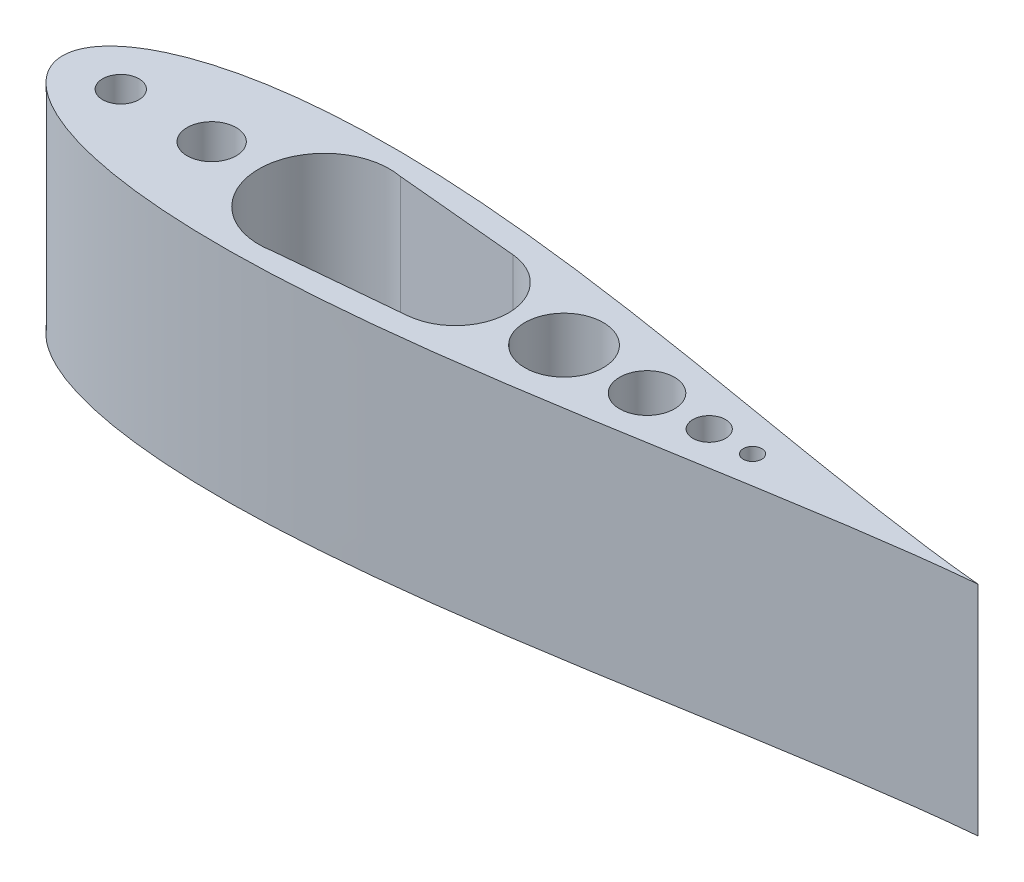
SolidWorks part; units mm, degrees
ref_plane "Front Plane" through (0, 0, 0) normal (0, 0, 1) x (1, 0, 0)
ref_plane "Top Plane" through (0, 0, 0) normal (0, 1, 0) x (1, 0, 0)
ref_plane "Right Plane" through (0, 0, 0) normal (1, 0, 0) x (0, 0, -1)
sketch "Sketch1" plane through (0, 0, 0) normal (0, 1, 0) x (1, 0, 0)
  line L0 (106.2646, 9.0063) -> (64.0952, 9.0063)
  line L4 (64.0952, 9.0063) -> (56.3694, 9.0063)
  line L5 (52.0514, 9.0063) -> (47.9363, 9.0063)
  line L6 (40.3163, 9.0063) -> (36.0359, 9.0063)
  line L7 (23.2512, 9.0063) -> (19.4412, 9.0063)
  line L8 (1.1792, 9.0063) -> (-2.6308, 9.0063)
  line L9 (-27.3546, 9.0063) -> (-31.1646, 9.0063)
  line L10 (-59.9171, 9.0063) -> (-65.1664, 9.0063)
  line L11 (-78.3744, 9.0063) -> (-87.6454, 9.0063)
  line L15 (-87.6454, 9.0063) -> (-88.7038, 9.0063)
  line L16 (-97.1704, 0) -> (-106.483, 0)
  line L17 (-45.5408, 15.24) -> (-13.8473, 12.2851)
  line L19 (-55, 0) -> (55, 0) construction
  line L20 (-45.5408, -15.24) -> (-13.8473, -12.2851)
  circle A1 centre (54.2104, 0) radius 2.159
  circle A2 centre (44.1263, 0) radius 3.81
  circle A3 centre (29.6435, 0) radius 6.3923
  circle A4 centre (10.3102, 0) radius 9.131
  arc A5 (-13.8473, -12.2851) -> (-13.8473, 12.2851) centre (-14.9927, 0) ccw
  arc A6 (-42.7236, 14.9773) -> (-42.7236, -14.9773) centre (-45.5408, 0) ccw
  circle A7 centre (-71.7704, 0) radius 5.715
  circle A8 centre (-92.9371, 0) radius 4.2333
  spline S0 degree 3 poles (-106.483, 0) (-106.482, -0.3362) (-106.4279, -1.1725) (-106.106, -2.6431) (-105.314, -4.4752) (-103.8975, -6.5043) (-101.808, -8.5717) (-99.0667, -10.5676) (-95.7198, -12.4267) (-91.8173, -14.1114) (-87.4067, -15.5993) (-82.5319, -16.8771) (-77.2341, -17.9374) (-71.5526, -18.7767) (-65.5251, -19.3955) (-59.1886, -19.7966) (-52.5791, -19.9863) (-45.732, -19.9729) (-38.6824, -19.7673) (-31.4645, -19.3826) (-24.1123, -18.8333) (-16.6591, -18.136) (-9.1376, -17.3083) (-1.5801, -16.3689) (5.9818, -15.3372) (13.5169, -14.233) (20.9946, -13.0761) (28.385, -11.8862) (35.6583, -10.6823) (42.7857, -9.4828) (49.7386, -8.3046) (56.4893, -7.1638) (63.0103, -6.0744) (69.2751, -5.0488) (75.2578, -4.0977) (80.9333, -3.2293) (86.2777, -2.4498) (91.2676, -1.7633) (95.8816, -1.1712) (100.0981, -0.6731) (103.6732, -0.2905) (105.8361, -0.0817) (106.7334, 0) knots 0.5 0.5 0.5 0.5 0.502167 0.50539 0.509656 0.514948 0.521245 0.528521 0.536745 0.545881 0.555891 0.56673 0.578353 0.59071 0.603747 0.61741 0.631639 0.646374 0.661552 0.677107 0.692975 0.709086 0.725371 0.741762 0.758188 0.774579 0.790865 0.806976 0.822844 0.8384 0.853578 0.868314 0.882544 0.896207 0.909245 0.921603 0.933227 0.944068 0.95408 0.963219 0.971447 0.977251 0.977251 0.977251 0.977251
  spline S1 degree 3 poles (-106.483, 0) (-106.482, 0.3362) (-106.4279, 1.1725) (-106.106, 2.6431) (-105.314, 4.4752) (-103.8975, 6.5043) (-101.808, 8.5717) (-99.0667, 10.5676) (-95.7198, 12.4267) (-91.8173, 14.1114) (-87.4067, 15.5993) (-82.5319, 16.8771) (-77.2341, 17.9374) (-71.5526, 18.7767) (-65.5251, 19.3955) (-59.1886, 19.7966) (-52.5791, 19.9863) (-45.732, 19.9729) (-38.6824, 19.7673) (-31.4645, 19.3826) (-24.1123, 18.8333) (-16.6591, 18.136) (-9.1376, 17.3083) (-1.5801, 16.3689) (5.9818, 15.3372) (13.5169, 14.233) (20.9946, 13.0761) (28.385, 11.8862) (35.6583, 10.6823) (42.7857, 9.4828) (49.7386, 8.3046) (56.4893, 7.1638) (63.0103, 6.0744) (69.2751, 5.0488) (75.2578, 4.0977) (80.9333, 3.2293) (86.2777, 2.4498) (91.2676, 1.7633) (95.8816, 1.1712) (100.0981, 0.6731) (103.6732, 0.2905) (105.8361, 0.0817) (106.7334, 0) knots 0.5 0.5 0.5 0.5 0.502167 0.50539 0.509656 0.514948 0.521245 0.528521 0.536745 0.545881 0.555891 0.56673 0.578353 0.59071 0.603747 0.61741 0.631639 0.646374 0.661552 0.677107 0.692975 0.709086 0.725371 0.741762 0.758188 0.774579 0.790865 0.806976 0.822844 0.8384 0.853578 0.868314 0.882544 0.896207 0.909245 0.921603 0.933227 0.944068 0.95408 0.963219 0.971447 0.977251 0.977251 0.977251 0.977251
  dimension "D1" = 11.43
  dimension "D2" = 30.48
extrude "Boss-Extrude1" add sketch "Sketch1" along normal blind 50.8
